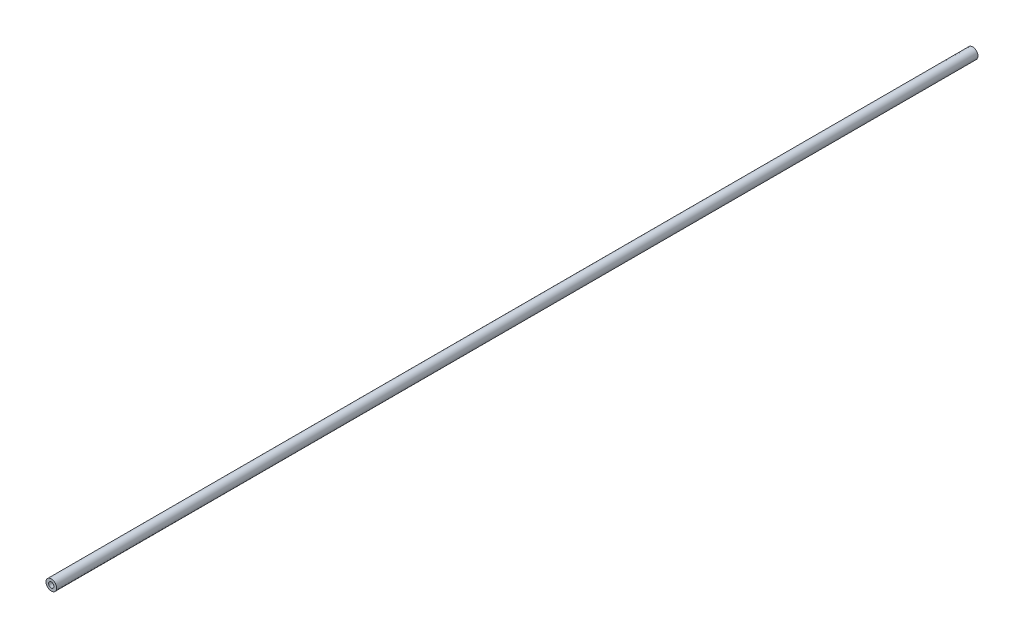
SolidWorks part; units mm, degrees
ref_plane "Front Plane" through (0, 0, 0) normal (0, 0, 1) x (1, 0, 0)
ref_plane "Top Plane" through (0, 0, 0) normal (0, 1, 0) x (1, 0, 0)
ref_plane "Right Plane" through (0, 0, 0) normal (1, 0, 0) x (0, 0, -1)
sketch "Sketch2" plane through (0, 0, 0) normal (0, 0, 1) x (1, 0, 0)
  circle A0 centre (0, 0) radius 2.54
  circle A1 centre (0, 0) radius 1.27
  dimension "D1" = 5.08
  dimension "D2" = 2.54
extrude "Boss-Extrude1" add sketch "Sketch2" along normal blind 441.96
